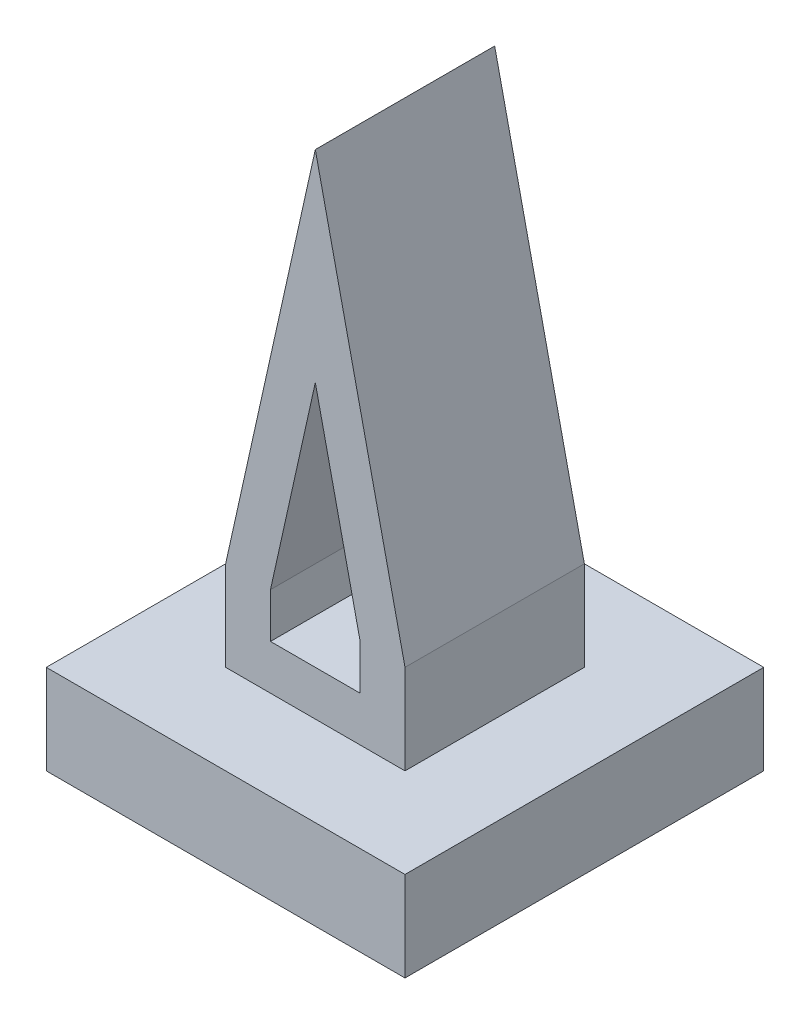
SolidWorks part; units mm, degrees
other "Perspective"
ref_plane "Front Plane" through (0, 0, 0) normal (0, 0, 1) x (1, 0, 0)
ref_plane "Top Plane" through (0, 0, 0) normal (0, 1, 0) x (1, 0, 0)
ref_plane "Right Plane" through (0, 0, 0) normal (1, 0, 0) x (0, 0, -1)
sketch "Sketch1" plane through (0, 0, 0) normal (0, 1, 0) x (1, 0, 0)
  line L1 (0, 0) -> (-80, 0)
  line L2 (0, 0) -> (0, 80)
  line L3 (0, 80) -> (-80, 80)
  line L4 (-80, 0) -> (-80, 80)
  dimension "D1" = 80
  dimension "D2" = 80
extrude "Extrude1" add sketch "Sketch1" along normal blind 20
sketch "Sketch2" plane through (0, 20, 0) normal (0, 1, 0) x (1, 0, 0)
  line L0 (0, 0) -> (0, 80) construction
  line L1 (-60, 60) -> (-20, 60)
  line L2 (-60, 60) -> (-60, 20)
  line L3 (-60, 20) -> (-20, 20)
  line L4 (-20, 60) -> (-20, 20)
  line L5 (-80, 0) -> (0, 0) construction
  dimension "D1" = 40
  dimension "D2" = 40
  dimension "D3" = 20
  dimension "D4" = 20
extrude "Extrude2" add sketch "Sketch2" along normal blind 110
sketch "Sketch3" plane through (0, 0, -20) normal (0, 0, 1) x (1, 0, 0)
  line L0 (-20, 40) -> (-40, 130)
  line L1 (-20, 130) -> (-20, 20) construction
  line L2 (-60, 130) -> (-20, 130) construction
  line L3 (-40, 130) -> (-60, 40)
  line L4 (-60, 130) -> (-60, 20) construction
  line L5 (-60, 40) -> (-60, 130)
  line L6 (-60, 130) -> (-20, 130)
  line L7 (-20, 130) -> (-20, 40)
  line L8 (-40, 85) -> (-30, 40)
  line L9 (-30, 40) -> (-30, 30)
  line L10 (-30, 30) -> (-50, 30)
  line L11 (-50, 30) -> (-50, 40)
  line L12 (-50, 40) -> (-40, 85)
  line L13 (-40, 130) -> (-40, 85) construction
  line L14 (-80, 20) -> (0, 20) construction
  line M2 (-20, 20) -> (-20, 130)
  line M3 (-20, 130) -> (-60, 130)
  line M4 (-60, 130) -> (-60, 20)
  dimension "D1" = 90
  dimension "D2" = 90
  dimension "D3" = 10
  dimension "D4" = 20
  dimension "D5" = 10
  dimension "D6" = 20
extrude "Extrude3" cut sketch "Sketch3" against normal blind 110 contours L3 M3 M4 | L0 M2 M3 | L12 L11 L10 L9 L8
